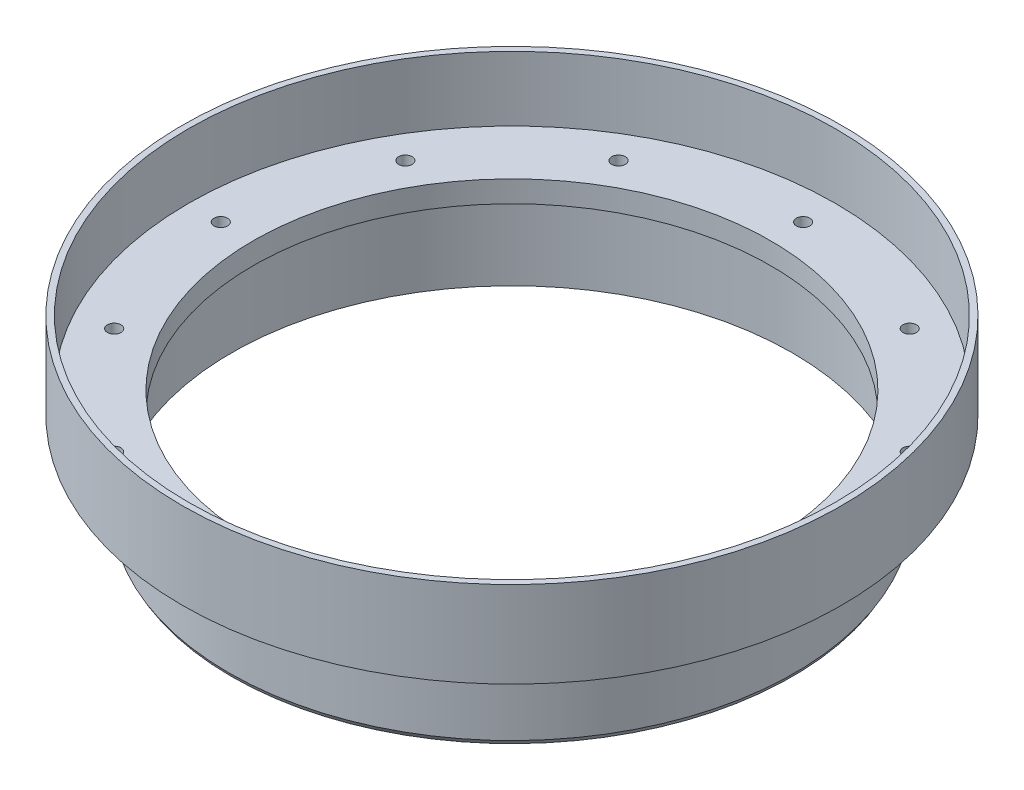
SolidWorks part; units mm, degrees
material "6061-T6 (SS)"
ref_plane "Front Plane" through (0, 0, 0) normal (0, 0, 1) x (1, 0, 0)
ref_plane "Top Plane" through (0, 0, 0) normal (0, 1, 0) x (1, 0, 0)
ref_plane "Right Plane" through (0, 0, 0) normal (1, 0, 0) x (0, 0, -1)
ref_axis "Axis1" through (0, 55, 0) along (0, -1, 0)
sketch "Cross Section" plane through (0, 0, 0) normal (0, 0, 1) x (1, 0, 0)
  line L0 (-38.1, 0) -> (-38.1, -3.175)
  line L1 (-38.1, -3.175) -> (-41.275, -3.175)
  line L2 (-41.275, -3.175) -> (-41.275, -15.875)
  line L3 (-41.275, -15.875) -> (-41.656, -15.2151)
  line L4 (0, -15.875) -> (-38.1, -15.875) construction
  line L5 (-41.656, -15.2151) -> (-41.656, -3.175)
  line L6 (-41.656, -3.175) -> (-48.514, -3.175)
  line L7 (-48.514, -3.175) -> (-48.514, 9.525)
  line L8 (-48.514, 9.525) -> (-47.625, 9.525)
  line L9 (-47.625, 9.525) -> (-47.625, 0)
  line L10 (-47.625, 0) -> (-38.1, 0)
  line L11 (-38.1, 0) -> (0, 0) construction
  line L12 (0, 55) -> (0, -55) construction
  line L14 (-47.625, 1.5875) -> (-47.625, 3.175) construction
  dimension "D1" = 3.175
  dimension "D3" = 0.381
  dimension "D4" = 30
  dimension "D5" = 6.858
  dimension "D6" = 12.7
  dimension "D9" = 3.175
  dimension "D8" = 38.1
revolve "Main" add sketch "Cross Section" angle 360 about axis through (0, 55, 0) along (0, -1, 0)
sketch "Hole Location" plane through (0, 0, 0) normal (0, 1, 0) x (1, 0, 0)
  line L0 (0, 0) -> (-42.8625, 0) construction
  circle A0 centre (0, 0) radius 42.8625 construction
  dimension "D1" = 85.725
hole_wizard "#3-48 Tapped Hole1" positions "Sketch5" profile "Sketch7" tap size "#3-48" standard "ANSI Inch"
sketch "Sketch5" plane through (0, 0, 0) normal (0, 1, 0) x (1, 0, 0)
  point P0 (-42.8625, 0)
sketch "Sketch7" plane through (-42.8625, 0, 0) normal (1, 0, 0) x (0, 0, 1)
  line L0 (0, 0) -> (0, 3.901)
  line L1 (0, 3.901) -> (0.9969, 3.302)
  line L2 (0.9969, 3.302) -> (0.9969, 0)
  line L5 (0.9969, 0) -> (0, 0)
  line L10 (0, 3.901) -> (-0.997, 3.302) construction
  line L11 (0, -6.35) -> (0, 107.95) construction
  dimension "Tap Drill Dia." = 1.9939
  dimension "Tap Drill Depth" = 3.302
  dimension "Drill Angle" = 118
cosmetic thread "Hole Thread1" parameters "D1"=3.175, "D2"=2.5146
pattern_circular "Screw Holes" count 12 over 360 about axis through (0, 0, 0) along (0, 1, 0) of "#3-48 Tapped Hole1"
equation "\"D8@Cross Section\"=\"TANK DIAMETER@Cryo Tank.Assembly\"/2"
equation "\"D1@Hole Location\"=\"TANK DIAMETER@Cryo Tank.Assembly\"+\"GASKET SEAT THICKNESS@Cryo Tank.Assembly\""
equation "\"D1@Cross Section\"=\"LINER THICKNESS@Cryo Tank.Assembly\""
equation "\"D3@Cross Section\"=\"ALUMINUM LAP THICKNESS@Cryo Tank.Assembly\""
equation "\"D5@Cross Section\"=2*\"CF THICKNESS@Cryo Tank.Assembly\"+\"NOMEX THICKNESS@Cryo Tank.Assembly\""
